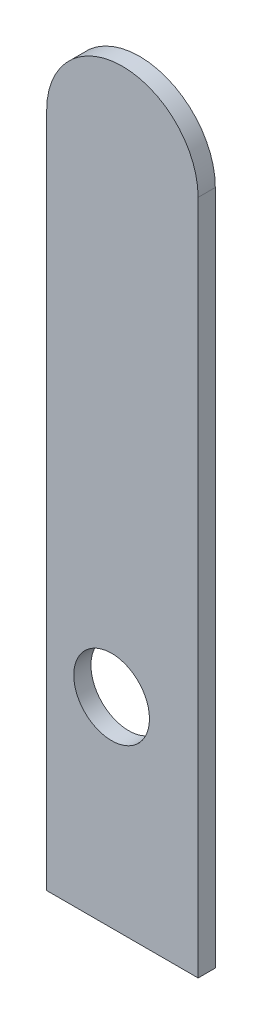
SolidWorks part; units mm, degrees
ref_plane "Front Plane" through (0, 0, 0) normal (0, 0, 1) x (1, 0, 0)
ref_plane "Top Plane" through (0, 0, 0) normal (0, 1, 0) x (1, 0, 0)
ref_plane "Right Plane" through (0, 0, 0) normal (1, 0, 0) x (0, 0, -1)
sketch "Model" plane through (0, 0, 0) normal (0, 0, 1) x (1, 0, 0)
  line L0 (0, 0) -> (0, 62.5)
  line L1 (14, 62.5) -> (14, 0)
  line L2 (14, 0) -> (0, 0)
  circle A0 centre (6, 18.5) radius 3.5
  arc A1 (14, 62.5) -> (0, 62.5) centre (7, 62.5) ccw
extrude "Boss-Extrude1" add sketch "Model" along normal blind 1.5875
